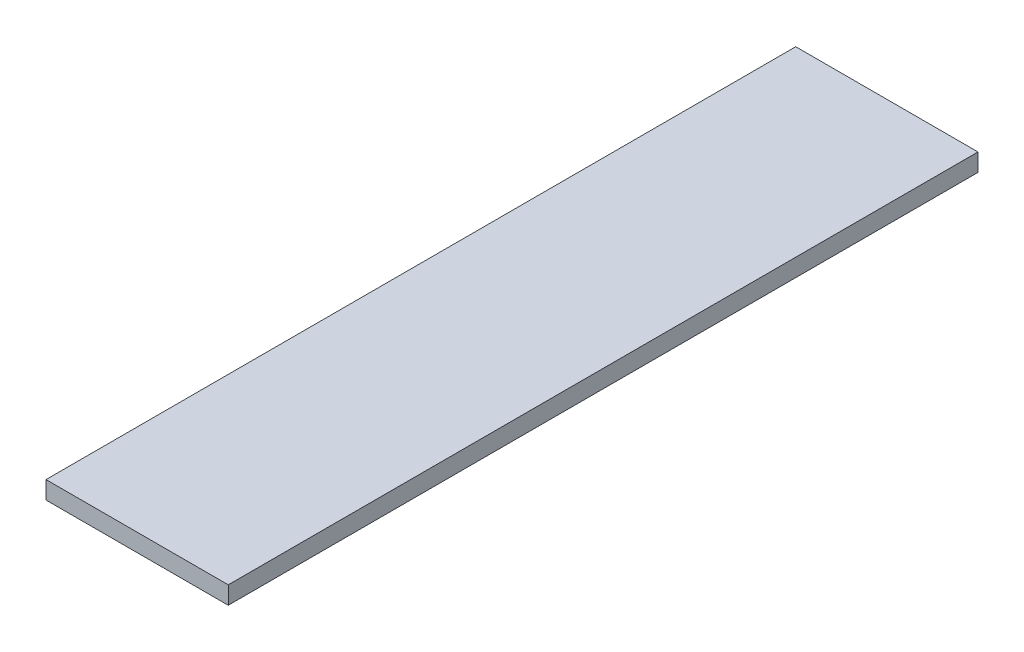
SolidWorks part; units mm, degrees
ref_plane "Спереди" through (0, 0, 0) normal (0, 0, 1) x (1, 0, 0)
ref_plane "Сверху" through (0, 0, 0) normal (0, 1, 0) x (1, 0, 0)
ref_plane "Справа" through (0, 0, 0) normal (1, 0, 0) x (0, 0, -1)
sketch "Эскиз1" plane through (0, 0, 0) normal (0, 1, 0) x (1, 0, 0)
  line L1 (92.5, -380.5) -> (-92.5, -380.5)
  line L2 (92.5, -380.5) -> (92.5, 380.5)
  line L3 (92.5, 380.5) -> (-92.5, 380.5)
  line L4 (-92.5, -380.5) -> (-92.5, 380.5)
  line L5 (92.5, -380.5) -> (-92.5, 380.5) construction
  line L6 (92.5, 380.5) -> (-92.5, -380.5) construction
  point P0 (0, 0)
  dimension "D1" = 185
  dimension "D2" = 761
extrude "Бобышка-Вытянуть1" add sketch "Эскиз1" along normal blind 18
